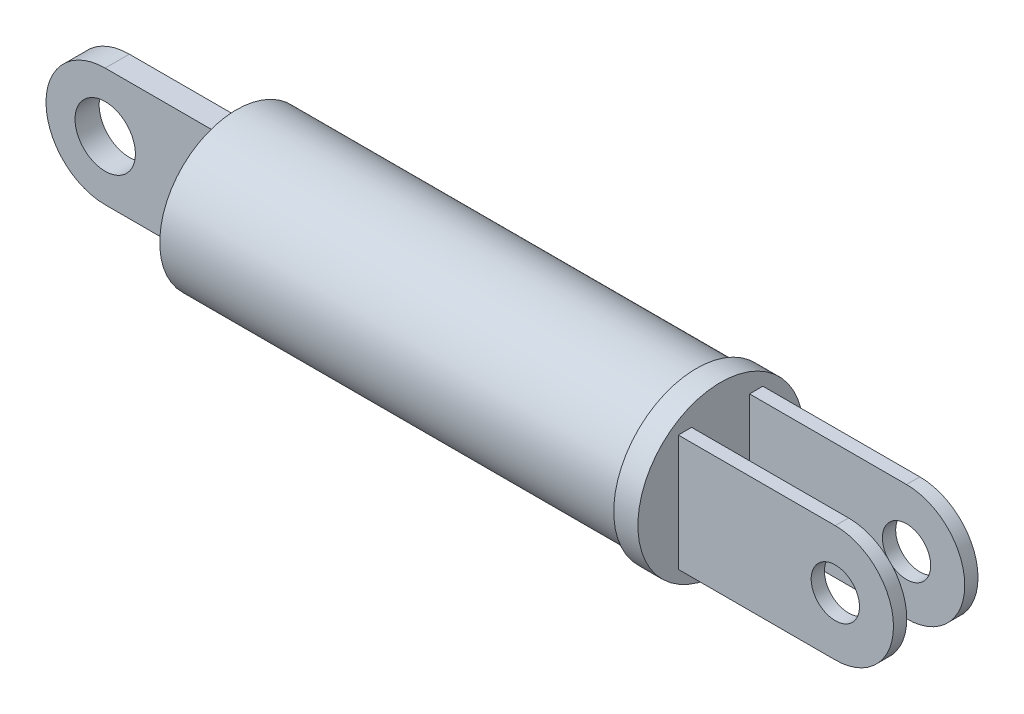
SolidWorks part; units mm, degrees
material "Cast Stainless Steel"
ref_plane "Front Plane" through (0, 0, 0) normal (0, 0, 1) x (1, 0, 0)
ref_plane "Top Plane" through (0, 0, 0) normal (0, 1, 0) x (1, 0, 0)
ref_plane "Right Plane" through (0, 0, 0) normal (1, 0, 0) x (0, 0, -1)
sketch "Sketch1" plane through (0, 0, 0) normal (1, 0, 0) x (0, 0, -1)
  circle A0 centre (0, 0) radius 12.7
  dimension "D1" = 25.4
extrude "Extrude1" add sketch "Sketch1" along normal blind 76.2
sketch "Sketch2" plane through (0, 0, 0) normal (0, 0, 1) x (1, 0, 0)
  line L0 (0, 0) -> (-32.8673, 0) construction
  line L1 (55, 0) -> (-55, 0) construction
  line L2 (0, 9.8057) -> (-19.7331, 9.8057)
  line L3 (0, 12.7) -> (0, -12.7) construction
  line L4 (0, -9.8057) -> (-19.7331, -9.8057)
  line L5 (0, 9.8057) -> (0, -9.8057)
  arc A0 (-19.7331, 9.8057) -> (-19.7331, -9.8057) centre (-19.7331, 0) ccw
  circle A1 centre (-19.7331, 0) radius 5
  dimension "D1" = 10
extrude "Extrude2" add sketch "Sketch2" along normal mid plane 4
sketch "Sketch3" plane through (76.2, 0, 0) normal (1, 0, 0) x (0, 0, -1)
  circle A2 centre (0, 0) radius 13.7
  circle A3 centre (0, 0) radius 13.7
  dimension "D1" = 1
extrude "Extrude3" add sketch "Sketch3" along normal blind 4
sketch "Sketch4" plane through (0, 0, 0) normal (0, 0, 1) x (1, 0, 0)
  line L0 (80.2, 9.6357) -> (106.2, 9.6357)
  line L1 (80.2, -13.7) -> (80.2, 13.7) construction
  line L2 (331.2897, 0) -> (364.956, 0) construction
  line L3 (80.2, -9.6357) -> (106.2, -9.6357)
  line L4 (80.2, 9.6357) -> (80.2, -9.6357)
  arc A0 (106.2, 9.6357) -> (106.2, -9.6357) centre (106.2, 0) cw
  circle A1 centre (106.2, 0) radius 4
  dimension "D1" = 8
  dimension "D2" = 26
extrude "Extrude4" add sketch "Sketch4" along normal mid plane 14
sketch "Sketch5" plane through (0, 0, 0) normal (0, 1, 0) x (1, 0, 0)
  line L0 (302.6802, 0) -> (363.3519, 0) construction
  line L1 (-15.07, 0) -> (15.07, 0) construction
  line L2 (80.2, -13.7) -> (80.2, 13.7) construction
  line L3 (80.2, 4.8012) -> (359.728, 4.8012)
  line L4 (80.2, 4.8012) -> (80.2, -4.8012)
  line L5 (80.2, -4.8012) -> (359.728, -4.8012)
  line L6 (359.728, 4.8012) -> (359.728, -4.8012)
  line L7 (359.728, 0) -> (80.2, 0) construction
extrude "Cut-Extrude1" cut sketch "Sketch5" against normal through all and the other way through all
